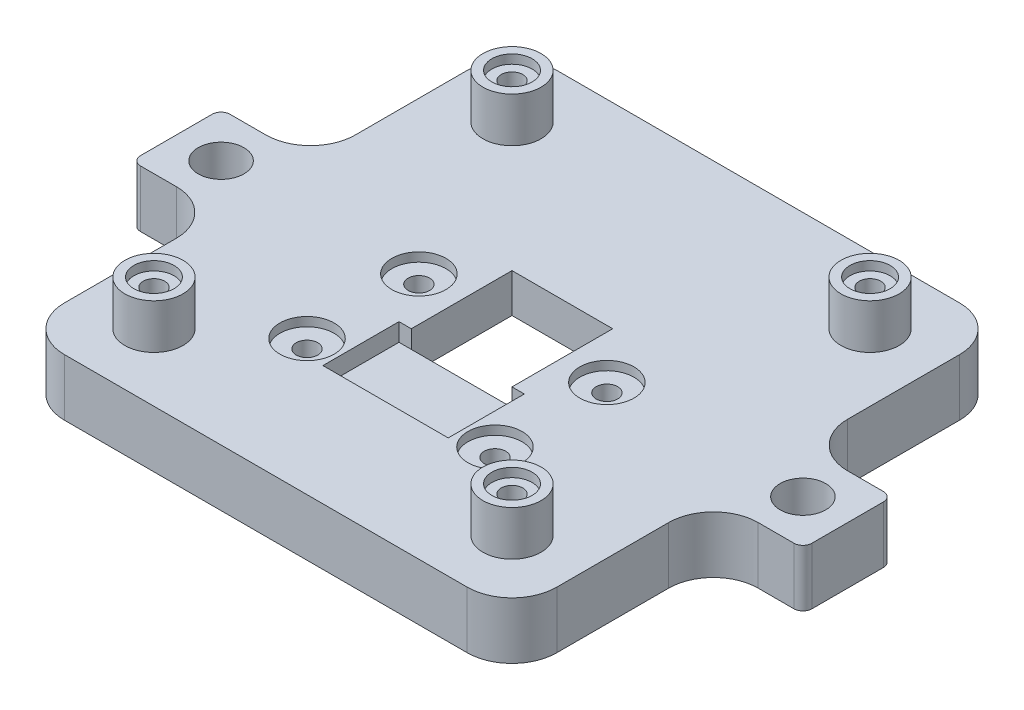
SolidWorks part; units mm, degrees
ref_plane "Front Plane" through (0, 0, 0) normal (0, 0, 1) x (1, 0, 0)
ref_plane "Top Plane" through (0, 0, 0) normal (0, 1, 0) x (1, 0, 0)
ref_plane "Right Plane" through (0, 0, 0) normal (1, 0, 0) x (0, 0, -1)
sketch "Sketch1" plane through (0, 0, 0) normal (0, 1, 0) x (1, 0, 0)
  line L1 (-27.5, 27.5) -> (27.5, 27.5)
  line L2 (-27.5, 27.5) -> (-27.5, -27.5)
  line L3 (-27.5, -27.5) -> (27.5, -27.5)
  line L4 (27.5, 27.5) -> (27.5, -27.5)
  line L5 (-27.5, 27.5) -> (27.5, -27.5) construction
  line L6 (-27.5, -27.5) -> (27.5, 27.5) construction
  point P0 (0, 0)
  dimension "D1" = 55
  dimension "D2" = 55
extrude "Boss-Extrude1" add sketch "Sketch1" along normal blind 6.35
sketch "Sketch2" plane through (0, 6.35, 0) normal (0, 1, 0) x (1, 0, 0)
  line L1 (-5.625, -5.625) -> (5.625, -5.625)
  line L2 (-5.625, -5.625) -> (-5.625, 5.625)
  line L3 (-5.625, 5.625) -> (5.625, 5.625)
  line L4 (5.625, -5.625) -> (5.625, 5.625)
  line L5 (-5.625, -5.625) -> (5.625, 5.625) construction
  line L6 (-5.625, 5.625) -> (5.625, -5.625) construction
  point P0 (0, 0)
  dimension "D1" = 11.25
extrude "Cut-Extrude1" cut sketch "Sketch2" against normal through all
sketch "Sketch3" plane through (0, 6.35, 0) normal (0, 1, 0) x (1, 0, 0)
  line L0 (0, 0) -> (0, 2.7158) construction
  line L1 (-7, -5.625) -> (7, -5.625)
  line L2 (-7, -5.625) -> (-7, -14.125)
  line L3 (-7, -14.125) -> (7, -14.125)
  line L4 (7, -5.625) -> (7, -14.125)
  line L6 (-5.625, -5.625) -> (5.625, -5.625) construction
  point P5 (0, -5.625)
  dimension "D1" = 14
  dimension "D2" = 8.5
extrude "Cut-Extrude2" cut sketch "Sketch3" against normal blind 2
sketch "Sketch4" plane through (0, 0, 0) normal (0, 1, 0) x (1, 0, 0)
  line L0 (0, 0) -> (0, 9.1234) construction
  line L2 (-12.5, 9.462) -> (12.5, 9.462) construction
  line L3 (-12.5, 9.462) -> (-12.5, -14.4) construction
  line L4 (-12.5, -14.4) -> (12.5, -14.4) construction
  line L5 (12.5, 9.462) -> (12.5, -14.4) construction
  point P7 (0, 9.462)
  point P8 (10.5, -12.4)
  point P9 (-10.5, -12.4)
  point P10 (-10.5, 0.1)
  point P11 (10.5, 0.1)
  dimension "D1" = 14.4
  dimension "D2" = 23.862
  dimension "D3" = 25
  dimension "D4" = 2
  dimension "D5" = 2
  dimension "D6" = 14.5
hole_wizard "CBORE for M2 SHCS2" positions "Sketch4" profile "Sketch15" counterbore size "M2" standard "ANSI Metric" end condition up to next
sketch "Sketch15" plane through (10.5, 0, -0.1) normal (1, 0, 0) x (0, 0, -1)
  line L0 (0, 0) -> (0, 6.35)
  line L1 (0, 6.35) -> (1.2, 6.35)
  line L3 (1.2, 6.35) -> (1.2, 2)
  line L4 (1.2, 2) -> (2.2, 2)
  line L5 (2.2, 2) -> (2.2, 0)
  line L7 (2.2, 0) -> (0, 0)
  line L11 (0, -6.35) -> (0, 107.95) construction
  dimension "Thru Hole Dia." = 2.4
  dimension "Thru Hole Depth" = 6.35
  dimension "C'Bore Dia." = 4.4
  dimension "C'Bore Depth" = 2
sketch "Sketch6" plane through (0, 6.35, 0) normal (0, 1, 0) x (1, 0, 0)
  line L1 (-20, -20) -> (20, -20) construction
  line L2 (-20, -20) -> (-20, 20) construction
  line L3 (-20, 20) -> (20, 20) construction
  line L4 (20, -20) -> (20, 20) construction
  line L5 (-20, -20) -> (20, 20) construction
  line L6 (-20, 20) -> (20, -20) construction
  circle A0 centre (-20, 20) radius 3.25
  circle A1 centre (20, 20) radius 3.25
  circle A2 centre (20, -20) radius 3.25
  circle A3 centre (-20, -20) radius 3.25
  point P0 (0, 0)
  dimension "D2" = 6.5
  dimension "D1" = 40
extrude "Boss-Extrude2" add sketch "Sketch6" along normal blind 5
sketch "Sketch10" plane through (0, 0, 0) normal (0, -1, 0) x (1, 0, 0)
  circle A0 centre (20, 20) radius 3.25 construction
  circle A1 centre (20, -20) radius 3.25 construction
  circle A2 centre (-20, -20) radius 3.25 construction
  circle A3 centre (-20, 20) radius 3.25 construction
  circle A4 centre (20, 20) radius 3.25 construction
  circle A5 centre (20, -20) radius 3.25 construction
  circle A6 centre (-20, -20) radius 3.25 construction
  circle A7 centre (-20, 20) radius 3.25 construction
  point P13 (-20, 20)
  point P14 (20, 20)
  point P15 (20, -20)
  point P16 (-20, -20)
hole_wizard "CBORE for M2 SHCS1" positions "Sketch10" profile "Sketch11" counterbore size "M2" standard "ANSI Metric" end condition through all
sketch "Sketch11" plane through (-20, 0, -20) normal (1, 0, 0) x (0, 0, -1)
  line L0 (0, 0) -> (0, 11.35)
  line L1 (0, 11.35) -> (1.2, 11.35)
  line L3 (1.2, 11.35) -> (1.2, 2)
  line L4 (1.2, 2) -> (2.2, 2)
  line L5 (2.2, 2) -> (2.2, 0)
  line L7 (2.2, 0) -> (0, 0)
  line L11 (0, -6.35) -> (0, 107.95) construction
  dimension "Thru Hole Dia." = 2.4
  dimension "Thru Hole Depth" = 11.35
  dimension "C'Bore Dia." = 4.4
  dimension "C'Bore Depth" = 2
sketch "Sketch12" plane through (0, 0, 0) normal (0, 0, 1) x (1, 0, 0)
  line L0 (27.5, 6.35) -> (27.5, 0) construction
  line L1 (-27.5, 6.35) -> (27.5, 6.35)
  line L2 (-27.5, 6.35) -> (-27.5, 11.35)
  line L3 (-27.5, 11.35) -> (27.5, 11.35)
  line L4 (27.5, 6.35) -> (27.5, 11.35)
  line L5 (-16.75, 11.35) -> (-23.25, 11.35) construction
extrude "Cut-Extrude3" [suppressed] cut sketch "Sketch12" against normal through all and the other way through all
sketch "Sketch13" plane through (0, 6.35, 0) normal (0, 1, 0) x (1, 0, 0)
  line L0 (0, 0) -> (0, -5.9289) construction
  circle A0 centre (-10.5, -12.4) radius 3.025
  circle A1 centre (-10.5, 0.1) radius 3.025
  circle A2 centre (10.5, -12.4) radius 3.025
  circle A3 centre (10.5, 0.1) radius 3.025
  circle A5 centre (-10.5, -12.4) radius 1.2 construction
  circle A6 centre (-10.5, 0.1) radius 1.2 construction
  dimension "D1" = 6.05
extrude "Cut-Extrude4" cut sketch "Sketch13" against normal blind 1
chamfer "Chamfer1" distance 2 angle 45 4 edges at (0, 0, -5.625) (5.625, 0, 0) (-5.625, 0, 0) (0, 0, 5.625)
sketch "Sketch14" plane through (0, 6.35, 0) normal (0, 1, 0) x (1, 0, 0)
  circle A0 centre (0, 0) radius 5.2973
sketch "Sketch16" plane through (0, 0, 0) normal (0, -1, 0) x (1, 0, 0)
  line L0 (0, 0) -> (30.2977, 0) construction
  line L1 (27.5, 27.5) -> (27.5, -27.5) construction
  line L2 (27.5, -5) -> (37.5, -5)
  line L3 (27.5, -5) -> (27.5, 5)
  line L4 (27.5, 5) -> (37.5, 5)
  line L5 (37.5, -5) -> (37.5, 5)
  line L6 (0, 0) -> (0, -32.0424) construction
  line L7 (-27.5, 5) -> (-37.5, 5)
  line L8 (-37.5, -5) -> (-37.5, 5)
  line L9 (-27.5, -5) -> (-37.5, -5)
  line L10 (-27.5, -5) -> (-27.5, 5)
  point P9 (27.5, 0)
  dimension "D1" = 10
  dimension "D2" = 10
extrude "Boss-Extrude3" add sketch "Sketch16" against normal up to surface (6.35 mm away) up to face at (-10.5, 6.35, 2.925)
sketch "Sketch17" plane through (0, 0, 0) normal (0, -1, 0) x (1, 0, 0)
  line L0 (37.5, 0) -> (27.5, 0) construction
  line L1 (37.5, -5) -> (37.5, 5) construction
  line L2 (27.5, -5) -> (27.5, -27.5) construction
  line L3 (0, 0) -> (0, -11.6553) construction
  circle A0 centre (32.5, 0) radius 2.55
  circle A1 centre (-32.5, 0) radius 2.55
  point P8 (32.5, 0)
  point P10 (-32.5, 0)
  point P17 (35.05, 0)
  dimension "D1" = 5.1
extrude "Cut-Extrude6" cut sketch "Sketch17" against normal through all
fillet "Fillet1" radius 5 8 edges at (27.5, 3.175, 5) (27.5, 3.175, -5) (-27.5, 3.175, 5) (-27.5, 3.175, -5) (-27.5, 3.175, -27.5) (-27.5, 3.175, 27.5) (27.5, 3.175, 27.5) (27.5, 3.175, -27.5)
fillet "Fillet2" radius 1 4 edges at (-37.5, 3.175, -5) (-37.5, 3.175, 5) (37.5, 3.175, 5) (37.5, 3.175, -5)
sketch "Sketch18" plane through (0, 11.35, 0) normal (0, 1, 0) x (1, 0, 0)
  circle A0 centre (-20, 20) radius 2.25
  circle A1 centre (-20, -20) radius 2.25
  circle A2 centre (20, 20) radius 2.25
  circle A3 centre (20, -20) radius 2.25
  dimension "D1" = 4.5
extrude "Cut-Extrude7" cut sketch "Sketch18" against normal blind 1
equation "\"D2@Sketch1\"=\"D1@Sketch1\""
